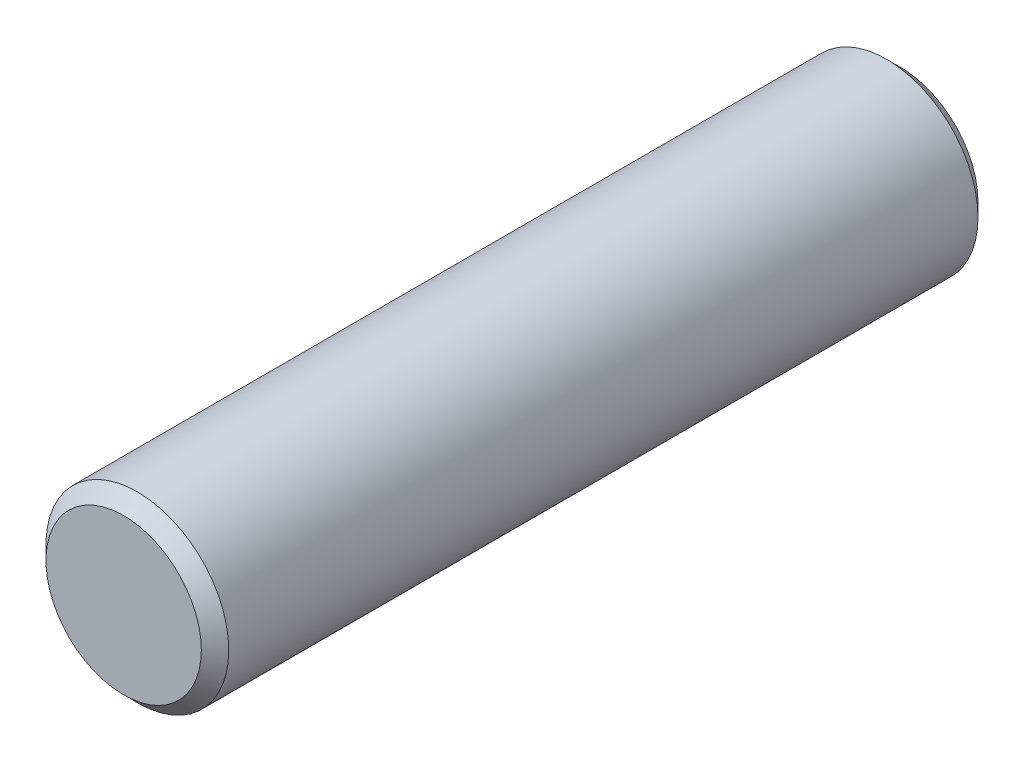
SolidWorks part; units mm, degrees
ref_plane "Front Plane" through (0, 0, 0) normal (0, 0, 1) x (1, 0, 0)
ref_plane "Top Plane" through (0, 0, 0) normal (0, 1, 0) x (1, 0, 0)
ref_plane "Right Plane" through (0, 0, 0) normal (1, 0, 0) x (0, 0, -1)
sketch "Sketch1" plane through (0, 0, 0) normal (0, 0, 1) x (1, 0, 0)
  circle A0 centre (0, 0) radius 2
  dimension "D1" = 4
extrude "Boss-Extrude1" add sketch "Sketch1" along normal blind 17
chamfer "Chamfer1" distance 0.3 angle 45 2 edges at (2, 0, 0) (2, 0, 17)
